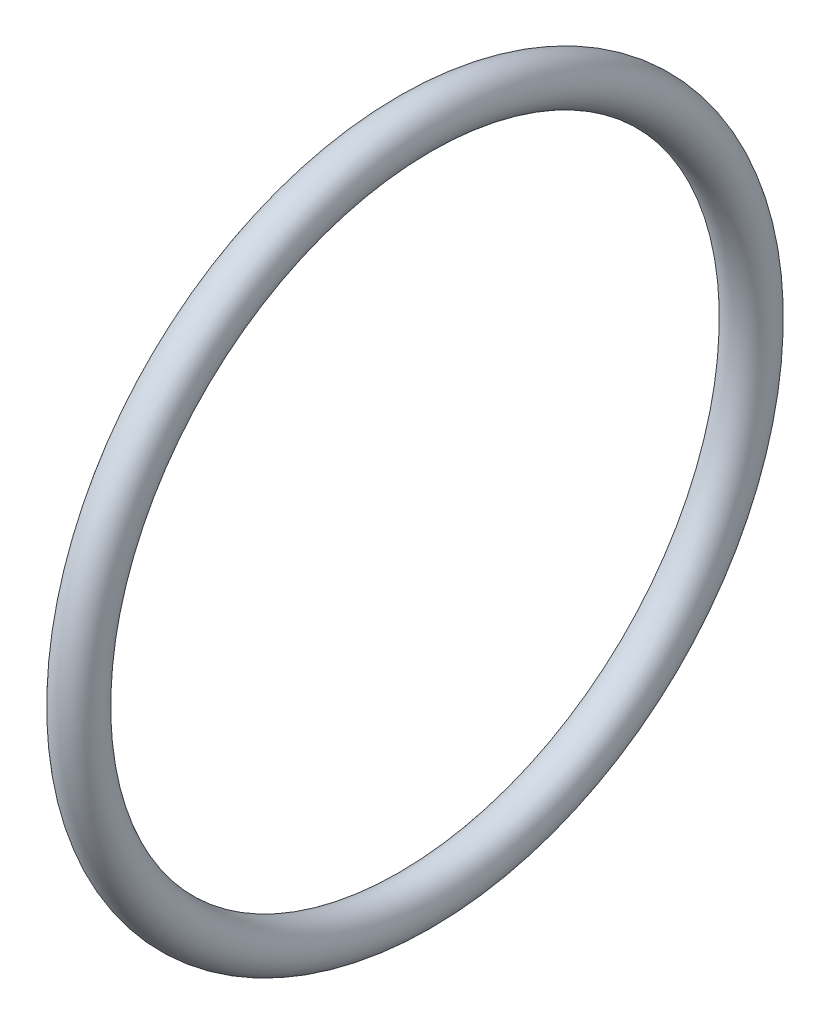
SolidWorks part; units mm, degrees
ref_plane "Alzado" through (0, 0, 0) normal (0, 0, 1) x (1, 0, 0)
ref_plane "Planta" through (0, 0, 0) normal (0, 1, 0) x (1, 0, 0)
ref_plane "Vista lateral" through (0, 0, 0) normal (1, 0, 0) x (0, 0, -1)
sketch "Croquis1" plane through (0, 0, 0) normal (0, 0, 1) x (1, 0, 0)
  circle A0 centre (0, -17.6784) radius 1.1906
  dimension "D1" = 2.3813
  dimension "OR" = 17.6784
sketch "Croquis2" plane through (0, 0, 0) normal (1, 0, 0) x (0, 0, -1)
  circle A0 centre (0, 0) radius 17.6784
  point P0 (0, 0)
  dimension "D1" = 35.3568
sweep "Barrer1" add profiles "Croquis1" path "Croquis2"
equation "\"OuterRadius\"= \"OuterDiameter\" / 2"
equation "\"OR@Croquis1\"=\"OuterRadius\""
equation "\"OuterDiameter\" = 1.392 * 25.4"
equation "\"NominalDiameter\"= ( 3 / 32 ) * 25.4"
equation "\"D1@Croquis1\"=\"NominalDiameter\""
equation "\"D1@Croquis2\"=\"OuterDiameter\""
